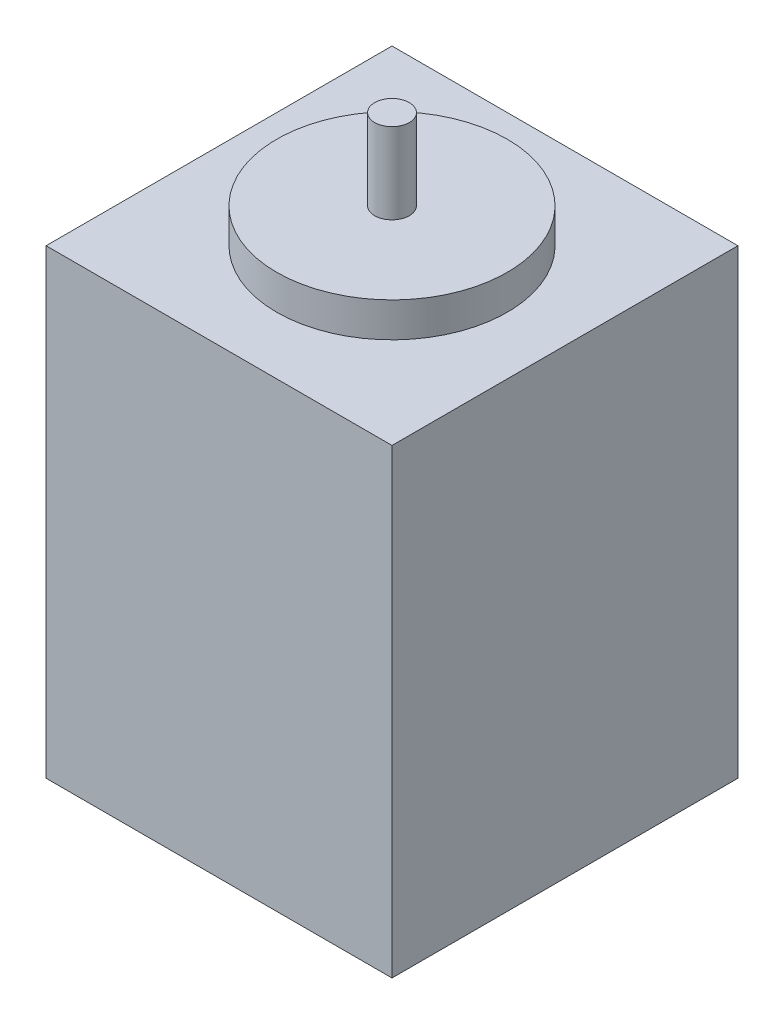
SolidWorks part; units mm, degrees
ref_plane "Front Plane" through (0, 0, 0) normal (0, 0, 1) x (1, 0, 0)
ref_plane "Top Plane" through (0, 0, 0) normal (0, 1, 0) x (1, 0, 0)
ref_plane "Right Plane" through (0, 0, 0) normal (1, 0, 0) x (0, 0, -1)
sketch "Sketch1" plane through (0, 0, 0) normal (0, 1, 0) x (1, 0, 0)
  line L1 (0, 0) -> (30, 0)
  line L2 (0, 0) -> (0, 30)
  line L3 (0, 30) -> (30, 30)
  line L4 (30, 0) -> (30, 30)
extrude "Boss-Extrude1" add sketch "Sketch1" along normal blind 40
sketch "Sketch2" plane through (0, 40, 0) normal (0, 1, 0) x (1, 0, 0)
  circle A0 centre (15, 15) radius 1.5
extrude "Boss-Extrude2" add sketch "Sketch2" along normal blind 10
sketch "Sketch4" plane through (0, 40, 0) normal (0, 1, 0) x (1, 0, 0)
  circle A0 centre (15, 15) radius 10
extrude "Boss-Extrude3" add sketch "Sketch4" along normal blind 3
